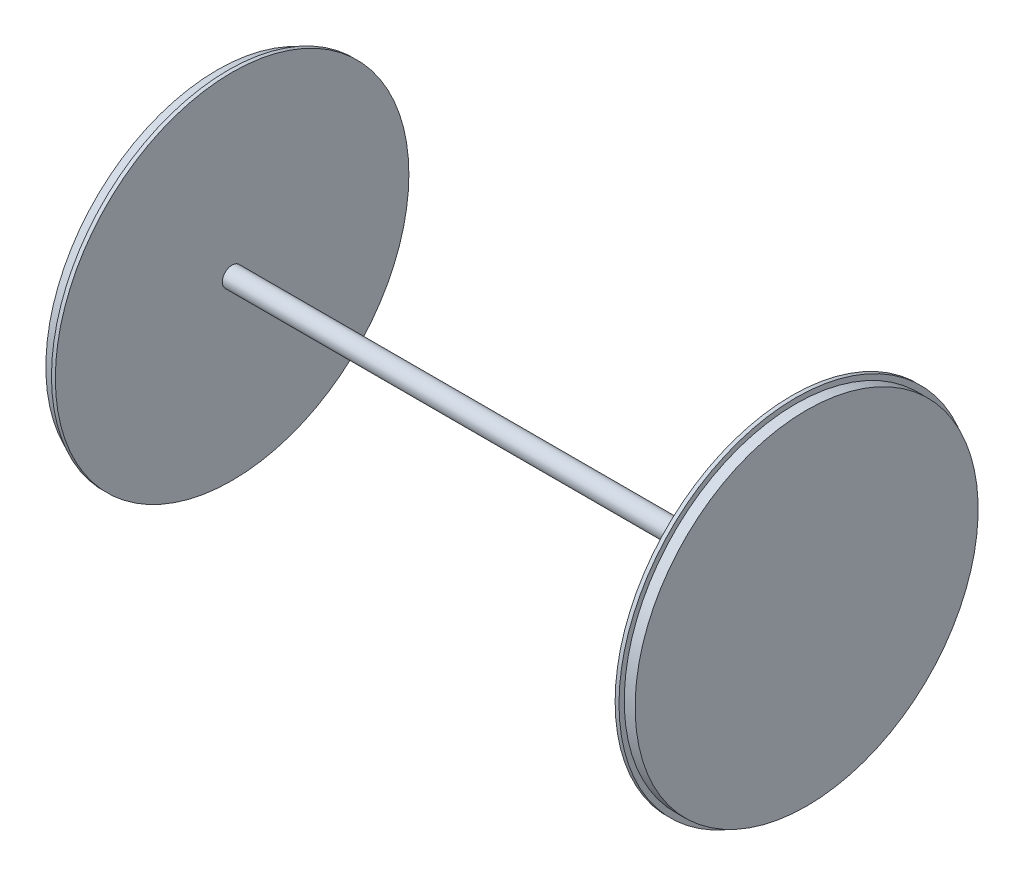
SolidWorks part; units mm, degrees
ref_plane "Front Plane" through (0, 0, 0) normal (0, 0, 1) x (1, 0, 0)
ref_plane "Top Plane" through (0, 0, 0) normal (0, 1, 0) x (1, 0, 0)
ref_plane "Right Plane" through (0, 0, 0) normal (1, 0, 0) x (0, 0, -1)
sketch "Sketch1" plane through (0, 0, 0) normal (0, 0, 1) x (1, 0, 0)
  line L0 (0, 0) -> (-3048, 0)
  line L1 (-3048, 0) -> (-3048, 887.22)
  line L2 (-2991.8, 914.4) -> (-2971.8, 914.4)
  line L3 (-2971.8, 914.4) -> (-2971.8, 50.8)
  line L4 (-2971.8, 50.8) -> (-76.2, 50.8)
  line L5 (-76.2, 50.8) -> (-76.2, 914.4)
  line L6 (-76.2, 914.4) -> (-56.2, 914.4)
  line L7 (0, 887.22) -> (0, 0)
  line L8 (-2991.8, 914.4) -> (-2991.8, 887.22)
  line L9 (-2991.8, 887.22) -> (-3048, 887.22)
  line L10 (-56.2, 914.4) -> (-56.2, 887.22)
  line L11 (-56.2, 887.22) -> (0, 887.22)
  line L12 (-2991.8, 887.22) -> (-56.2, 887.22) construction
  dimension "D1" = 50.8
revolve "Revolve2" add sketch "Sketch1" angle 360 about L0
